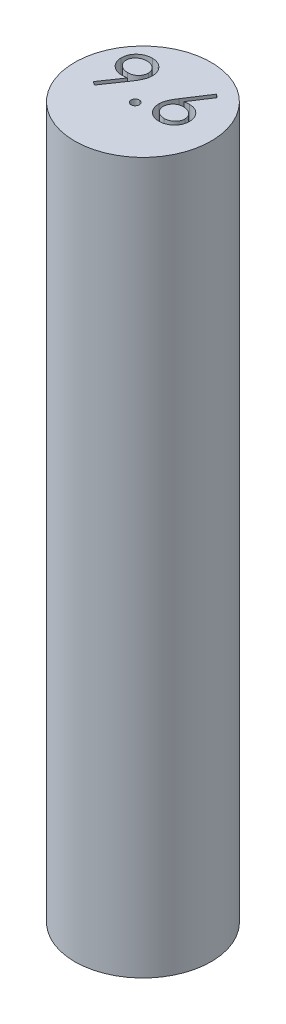
SolidWorks part; units mm, degrees
ref_plane "Front Plane" through (0, 0, 0) normal (0, 0, 1) x (1, 0, 0)
ref_plane "Top Plane" through (0, 0, 0) normal (0, 1, 0) x (1, 0, 0)
ref_plane "Right Plane" through (0, 0, 0) normal (1, 0, 0) x (0, 0, -1)
sketch "Sketch1" plane through (0, 0, 0) normal (0, 1, 0) x (1, 0, 0)
  circle A0 centre (0, 0) radius 4.8
  dimension "D1" = 9.6
extrude "Boss-Extrude1" add sketch "Sketch1" along normal blind 50
sketch "Sketch2" plane through (0, 50, 0) normal (0, 1, 0) x (1, 0, 0)
  line L0 (-4.6234, -0.6232) -> (4.4125, -0.4792) construction
  text T0 "9.6 "
extrude "Cut-Extrude1" cut sketch "Sketch2" against normal blind 3
